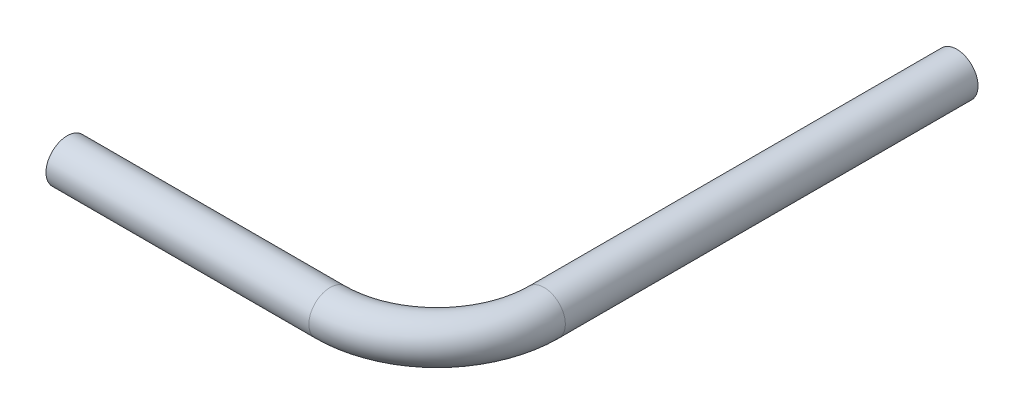
SolidWorks part; units mm, degrees
material "AISI 304"
ref_plane "Front Plane" through (0, 0, 0) normal (0, 0, 1) x (1, 0, 0)
ref_plane "Top Plane" through (0, 0, 0) normal (0, 1, 0) x (1, 0, 0)
ref_plane "Right Plane" through (0, 0, 0) normal (1, 0, 0) x (0, 0, -1)
sketch "Sketch3" plane through (0, 0, 0) normal (0, 1, 0) x (1, 0, 0)
  line L0 (0, 0) -> (39.3, 0)
  line L1 (55.3, 16) -> (55.3, 77.699)
  arc A0 (39.3, 0) -> (55.3, 16) centre (39.3, 16) ccw
  dimension "D1" = 55.3
  dimension "D2" = 16
  dimension "D3" = 77.699
sketch "Sketch2" plane through (0, 0, 0) normal (1, 0, 0) x (0, 0, -1)
  circle A0 centre (0, 0) radius 3.175
  dimension "D1" = 6.35
sweep "Sweep-Thin1" add profiles "Sketch2" path "Sketch3" parameters "D1"=0.7112
